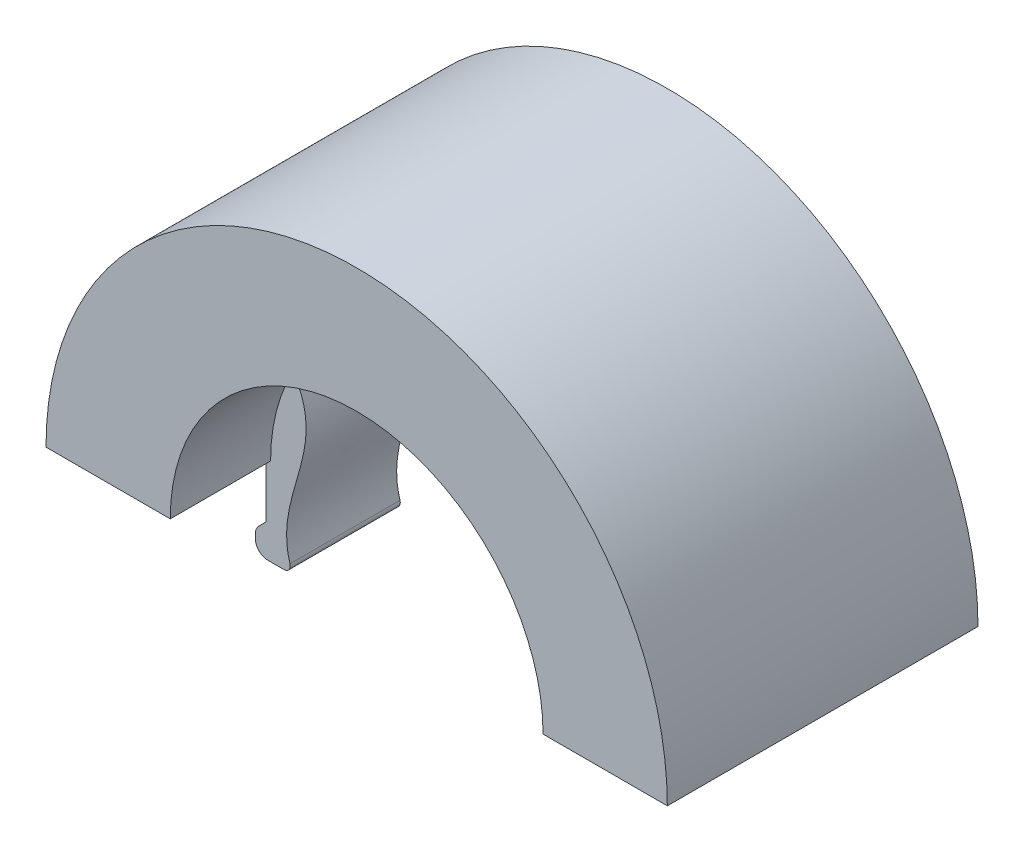
SolidWorks part; units mm, degrees
ref_plane "Front Plane" through (0, 0, 0) normal (0, 0, 1) x (1, 0, 0)
ref_plane "Top Plane" through (0, 0, 0) normal (0, 1, 0) x (1, 0, 0)
ref_plane "Right Plane" through (0, 0, 0) normal (1, 0, 0) x (0, 0, -1)
sketch "Sketch1" plane through (0, 0, 0) normal (0, 0, 1) x (1, 0, 0)
  line L0 (0, 0) -> (49.1339, 0) construction
  line L1 (49.1339, 0) -> (-47.428, 0) construction
  line L2 (-25, 0) -> (-15, 0)
  line L3 (15, 0) -> (25, 0)
  arc A0 (15, 0) -> (-15, 0) centre (0, 0) ccw
  arc A1 (25, 0) -> (-25, 0) centre (0, 0) ccw
  dimension "D1" = 50
  dimension "D2" = 30
extrude "Boss-Extrude1" add sketch "Sketch1" along normal mid plane 25 contours A1 L2 A0 L3
ref_plane "Plane1" through (0, 0, 12.5) normal (0, 0, 1) x (1, 0, 0)
sketch "Sketch2" plane through (0, 0, 12.5) normal (0, 0, 1) x (1, 0, 0)
  line L0 (-20, 0) -> (-20, -50000) construction
  line L1 (-25, 0) -> (-15, 0) construction
  line L2 (-22.625, 0) -> (-22.625, -50000) construction
  line L3 (-17.375, 0) -> (-17.375, -50000) construction
  line L4 (-22.625, 5.25) -> (-17.375, 5.25)
  line L5 (-22.625, 5.25) -> (-21.575, 0)
  line L6 (-21.575, 0) -> (-18.425, 0)
  line L7 (-18.425, 0) -> (-17.375, 5.25)
  point P4 (-20, 0)
  dimension "D1" = 2.625
  dimension "D2" = 2.625
  dimension "D3" = 5.25
  dimension "D4" = 1.575
  dimension "D5" = 1.575
ref_plane "Plane2" through (0, 0, 0) normal (0, 0, 1) x (1, 0, 0)
sketch "Sketch3" plane through (0, 0, 0) normal (0, 0, 1) x (1, 0, 0)
  line L1 (12.5557, 34.0493) -> (16.1731, 34.0493)
  line L4 (15.3827, 0) -> (15.3827, -4.45)
  line L5 (25, 0) -> (-25, 0) construction
  line L6 (13.6027, -10.031) -> (14.6027, -10.031) construction
  line L7 (13.75, 0) -> (-13.75, 0) construction
  line L8 (15.3827, 0) -> (15, 0)
  line L10 (13.2022, -7.031) -> (16.2282, -7.031)
  line L13 (16.2282, -7.031) -> (16.2282, -5.2955)
  line L14 (-983.3145, -10.031) -> (-10.5859, -10.031) construction
  line L15 (16.2282, -5.2955) -> (15.3827, -4.45)
  line L16 (15.3827, -4.45) -> (18.1469, -4.45) construction
  arc A0 (15, 0) -> (-15, 0) centre (0, 0) ccw construction
  arc A2 (15, 0) -> (13.2022, 7.1205) centre (0, 0) ccw
  arc A3 (25, 0) -> (-25, 0) centre (0, 0) ccw construction
  spline S0 degree 3 poles (13.2022, 7.1205) (9.9868, 2.4499) (15.31, -2.1824) (13.2022, -7.031) knots 0 0 0 0 1 1 1 1
  point P11 (14, -14.04)
  point P23 (0, 0)
  point P30 (0, 0)
  dimension "D4" = 0.3827
  dimension "D6" = 1.2282
  dimension "D7" = 0.8455
  dimension "D8" = 1.7355
extrude "Boss-Extrude3" add sketch "Sketch3" along normal mid plane 8.8555 contours L10 L13 L15 L4 L8 A2 S0
mirror "Mirror11" about plane through (0, 0, 0) normal (1, 0, 0) of "Boss-Extrude3"
fillet "Fillet1" radius 1 1 edges at (16.2282, -7.031, 0)
fillet "Fillet2" radius 1 1 edges at (-16.2282, -7.031, 0)
sketch "Sketch4" plane through (0, 0, 0) normal (0, -1, 0) x (1, 0, 0)
  line L0 (25, 0) -> (-49975, 0) construction
  line L1 (25, 12.5) -> (25, -12.5) construction
  line L3 (20, -7.5) -> (20, -50007.5) construction
  line L4 (15, -12.5) -> (25, -12.5) construction
  line L5 (31.0617, -4.5) -> (-49968.9383, -4.5) construction
  line L6 (31.715, 3.9639) -> (-49968.285, 3.9639) construction
  circle A0 centre (20, -4.5) radius 3.388
  circle A1 centre (20, 4.5) radius 3.388
  point P4 (25, 0)
  point P9 (20, -12.5)
  dimension "D1" = 6.776
  dimension "D2" = 8
fillet "Fillet5" radius 1 1 edges at (16.2282, -5.2955, 0)
fillet "Fillet6" radius 1 1 edges at (-16.2282, -5.2955, 0)
extrude "Cut-Extrude1" cut sketch "Sketch4" against normal blind 5.656
mirror "Mirror12" about plane through (0, 0, 0) normal (1, 0, 0) of "Cut-Extrude1"
fillet "Fillet7" radius 0.5 2 edges at (-13.2022, -7.031, 0) (13.2022, -7.031, 0)
